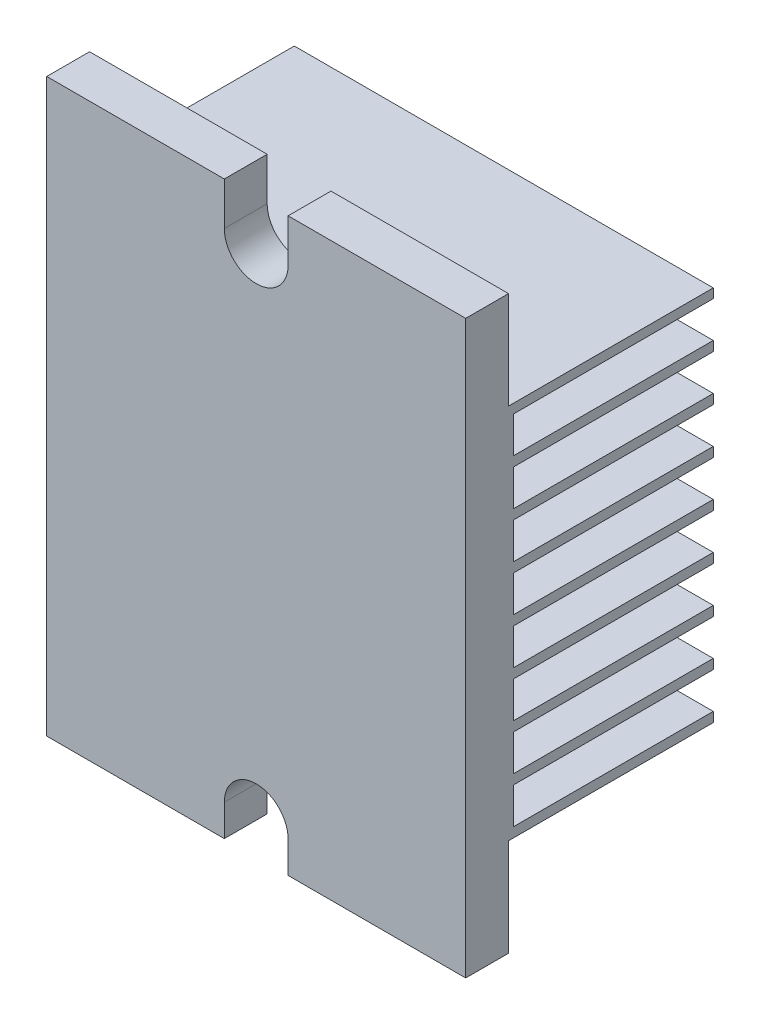
SolidWorks part; units mm, degrees
ref_plane "Piano frontale" through (0, 0, 0) normal (0, 0, 1) x (1, 0, 0)
ref_plane "Piano superiore" through (0, 0, 0) normal (0, 1, 0) x (1, 0, 0)
ref_plane "Piano destro" through (0, 0, 0) normal (1, 0, 0) x (0, 0, -1)
sketch "Schizzo1" plane through (0, 0, 0) normal (0, 0, 1) x (1, 0, 0)
  line L1 (-22, 30) -> (22, 30)
  line L2 (-22, 30) -> (-22, -30)
  line L3 (-22, -30) -> (22, -30)
  line L4 (22, 30) -> (22, -30)
  line L5 (-22, 30) -> (22, -30) construction
  line L6 (-22, -30) -> (22, 30) construction
  point P0 (0, 0)
  dimension "D1" = 44
  dimension "D2" = 60
extrude "Estrusione-Estrusione1" add sketch "Schizzo1" along normal blind 26
sketch "Schizzo2" plane through (-22, 0, 0) normal (-1, 0, 0) x (0, 0, 1)
  line L0 (0, 30) -> (0, -30) construction
  line L1 (0, -18.75) -> (21, -18.75)
  line L2 (0, -18.75) -> (0, -14.95)
  line L3 (0, -14.95) -> (21, -14.95)
  line L4 (21, -18.75) -> (21, -14.95)
  line L5 (26, -30) -> (0, -30) construction
  dimension "D1" = 3.8
  dimension "D2" = 21
  dimension "D3" = 11.25
extrude "Taglio-Estrusione1" cut sketch "Schizzo2" against normal through all
pattern_linear "Ripetizione a L1" count 8 spacing 4.82 along (0, 1, 0) of "Taglio-Estrusione1"
sketch "Schizzo3" plane through (22, 0, 0) normal (1, 0, 0) x (0, 0, -1)
  line L0 (0, 0) -> (-35.3514, 0) construction
  line L2 (0, -24.885) -> (-21.5, -24.885) construction
  line L3 (0, -30) -> (0, -18.75) construction
  line L4 (0, -18.75) -> (-21, -18.75) construction
  line L9 (-26, -30) -> (0, -30) construction
  line L10 (-21.5, 30) -> (0, 19.77) construction
  line L11 (-21.5, -19.77) -> (0, -19.77)
  line L12 (-21.5, -19.77) -> (-21.5, -30)
  line L13 (-21.5, -30) -> (0, -30)
  line L14 (0, -19.77) -> (0, -30)
  line L15 (-21.5, -19.77) -> (0, -30) construction
  line L16 (-21.5, -30) -> (0, -19.77) construction
  line L21 (-21.5, 19.77) -> (0, 30) construction
  line L22 (0, 24.885) -> (-21.5, 24.885) construction
  line L23 (0, 19.77) -> (0, 30)
  line L24 (-21.5, 30) -> (0, 30)
  line L25 (-21.5, 19.77) -> (-21.5, 30)
  line L26 (-21.5, 19.77) -> (0, 19.77)
  point P13 (-10.75, -24.885)
  point P25 (-10.75, 24.885)
  dimension "D1" = 21.5
  dimension "D2" = 1.02
extrude "Taglio-Estrusione2" cut sketch "Schizzo3" against normal through all
sketch "Schizzo5" plane through (0, 0, 21.5) normal (0, 0, -1) x (-1, 0, 0)
  line L0 (0, 34.5) -> (0, 25.5) construction
  line L1 (22, 30) -> (-22, 30) construction
  line L2 (3.35, 34.5) -> (3.35, 25.5)
  line L3 (-3.35, 34.5) -> (-3.35, 25.5)
  line L4 (0, -33.3138) -> (0, -26.6862) construction
  line L5 (22, -30) -> (-22, -30) construction
  line L6 (-3.35, -33.3138) -> (-3.35, -26.6862)
  line L7 (3.35, -33.3138) -> (3.35, -26.6862)
  arc A0 (3.35, 34.5) -> (-3.35, 34.5) centre (0, 34.5) ccw
  arc A1 (-3.35, 25.5) -> (3.35, 25.5) centre (0, 25.5) ccw
  arc A2 (-3.35, -33.3138) -> (3.35, -33.3138) centre (0, -33.3138) ccw
  arc A3 (3.35, -26.6862) -> (-3.35, -26.6862) centre (0, -26.6862) ccw
  point P5 (0, 30)
  point P11 (0, -30)
  dimension "D1" = 6.7
  dimension "D2" = 4.5
extrude "Taglio-Estrusione4" cut sketch "Schizzo5" against normal through all
